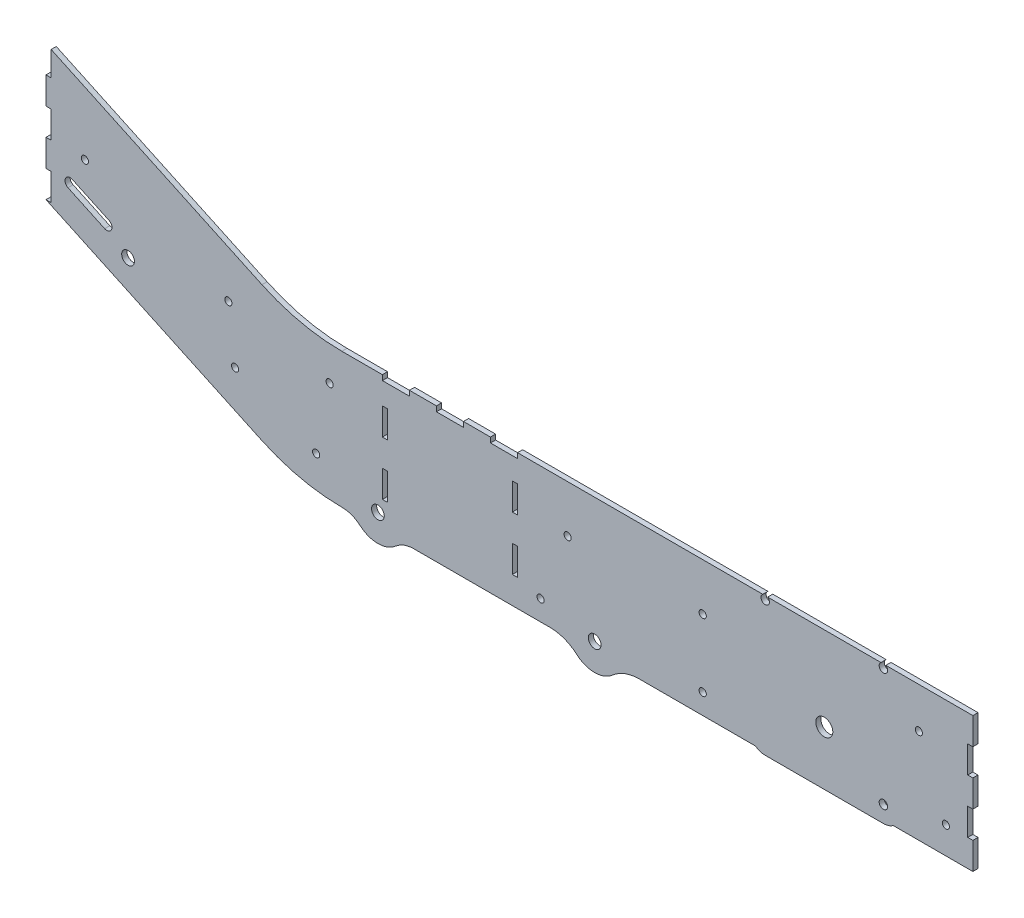
SolidWorks part; units mm, degrees
material "1060 Alloy"
ref_plane "Front Plane" through (0, 0, 0) normal (0, 0, 1) x (1, 0, 0)
ref_plane "Top Plane" through (0, 0, 0) normal (0, 1, 0) x (1, 0, 0)
ref_plane "Right Plane" through (0, 0, 0) normal (1, 0, 0) x (0, 0, -1)
sketch "Sketch1" plane through (0, 0, 0) normal (0, 0, 1) x (1, 0, 0)
  line L0 (255.5035, 390.3745) -> (331.7035, 390.3745)
  line L2 (-26.9148, 387.4343) -> (-61.4451, 403.5361)
  line L3 (-65.5242, 394.7884) -> (-30.9939, 378.6866)
  line L4 (-26.9148, 387.4343) -> (-61.4451, 403.5361)
  line L5 (-65.5242, 394.7884) -> (-30.9939, 378.6866)
  line L22 (790.1102, 263.3745) -> (790.1102, 288.7745)
  line L23 (790.1102, 288.7745) -> (785.2842, 288.7745)
  line L24 (785.2842, 288.7745) -> (785.2842, 314.1745)
  line L25 (785.2842, 314.1745) -> (790.1102, 314.1745)
  line L26 (790.1102, 314.1745) -> (790.1102, 339.5745)
  line L27 (790.1102, 339.5745) -> (785.2842, 339.5745)
  line L28 (785.2842, 339.5745) -> (785.2842, 364.9745)
  line L29 (785.2842, 364.9745) -> (790.1102, 364.9745)
  line L30 (790.1102, 364.9745) -> (790.1102, 390.3745)
  line L31 (790.1102, 390.3745) -> (331.7035, 390.3745)
  line L32 (116.862, 407.033) -> (-86.1898, 501.7176)
  line L33 (-86.1898, 501.7176) -> (-86.1898, 476.3176)
  line L34 (-86.1898, 476.3176) -> (-81.3638, 476.3176)
  line L35 (-81.3638, 476.3176) -> (-81.3638, 450.9176)
  line L36 (-81.3638, 450.9176) -> (-86.1898, 450.9176)
  line L37 (-86.1898, 450.9176) -> (-86.1898, 425.5176)
  line L38 (-86.1898, 425.5176) -> (-81.3638, 425.5176)
  line L39 (-81.3638, 425.5176) -> (-81.3638, 400.1176)
  line L40 (-81.3638, 400.1176) -> (-86.1898, 400.1176)
  line L41 (-86.1898, 400.1176) -> (-86.1898, 374.7176)
  line L42 (-86.1898, 374.7176) -> (116.862, 280.033)
  line L43 (666.755, 263.3745) -> (790.1102, 263.3745)
  line L44 (790.1102, 263.3745) -> (790.1102, 288.7745)
  line L45 (790.1102, 288.7745) -> (785.2842, 288.7745)
  line L46 (785.2842, 288.7745) -> (785.2842, 314.1745)
  line L47 (785.2842, 314.1745) -> (790.1102, 314.1745)
  line L48 (790.1102, 314.1745) -> (790.1102, 339.5745)
  line L49 (790.1102, 339.5745) -> (785.2842, 339.5745)
  line L50 (785.2842, 339.5745) -> (785.2842, 364.9745)
  line L51 (785.2842, 364.9745) -> (790.1102, 364.9745)
  line L52 (790.1102, 364.9745) -> (790.1102, 390.3745)
  line L53 (790.1102, 390.3745) -> (331.7035, 390.3745)
  line L54 (116.862, 407.033) -> (-86.1898, 501.7176)
  line L55 (-86.1898, 501.7176) -> (-86.1898, 476.3176)
  line L56 (-86.1898, 476.3176) -> (-81.3638, 476.3176)
  line L57 (-81.3638, 476.3176) -> (-81.3638, 450.9176)
  line L58 (-81.3638, 450.9176) -> (-86.1898, 450.9176)
  line L59 (-86.1898, 450.9176) -> (-86.1898, 425.5176)
  line L60 (-86.1898, 425.5176) -> (-81.3638, 425.5176)
  line L61 (-81.3638, 425.5176) -> (-81.3638, 400.1176)
  line L62 (-81.3638, 400.1176) -> (-86.1898, 400.1176)
  line L63 (-86.1898, 400.1176) -> (-86.1898, 374.7176)
  line L64 (-86.1898, 374.7176) -> (116.862, 280.033)
  line L65 (666.755, 263.3745) -> (790.1102, 263.3745)
  line L111 (259.7387, 263.3745) -> (387.7681, 263.3745)
  line L112 (259.7387, 263.3745) -> (387.7681, 263.3745)
  line L234 (471.6003, 263.3745) -> (624.4135, 263.3745)
  line L235 (471.6003, 263.3745) -> (624.4135, 263.3745)
  line L312 (306.3035, 385.5485) -> (306.3035, 390.3745)
  line L313 (306.3035, 385.5485) -> (306.3035, 390.3745) construction
  line L314 (306.3035, 390.3745) -> (280.9035, 390.3745)
  line L315 (306.3035, 390.3745) -> (280.9035, 390.3745)
  line L316 (280.9035, 390.3745) -> (280.9035, 385.5485)
  line L317 (280.9035, 390.3745) -> (280.9035, 385.5485) construction
  line L318 (280.9035, 385.5485) -> (255.5035, 385.5485)
  line L319 (280.9035, 385.5485) -> (255.5035, 385.5485) construction
  line L320 (255.5035, 385.5485) -> (255.5035, 390.3745)
  line L321 (255.5035, 385.5485) -> (255.5035, 390.3745) construction
  line L322 (255.5035, 390.3745) -> (192.0035, 390.3745)
  line L323 (255.5035, 390.3745) -> (192.0035, 390.3745)
  line L324 (331.7035, 390.3745) -> (331.7035, 385.5485)
  line L325 (331.7035, 390.3745) -> (331.7035, 385.5485) construction
  line L326 (331.7035, 385.5485) -> (306.3035, 385.5485)
  line L327 (331.7035, 385.5485) -> (306.3035, 385.5485) construction
  circle A1 centre (-51.9745, 393.795) radius 4.826
  arc A2 (116.862, 407.033) -> (192.0035, 390.3745) centre (192.0035, 568.1745) ccw
  arc A3 (116.862, 280.033) -> (192.0035, 263.3745) centre (192.0035, 441.1745) ccw
  arc A4 (116.862, 407.033) -> (192.0035, 390.3745) centre (192.0035, 568.1745) ccw
  arc A5 (116.862, 280.033) -> (192.0035, 263.3745) centre (192.0035, 441.1745) ccw
  circle A6 centre (-51.9745, 393.795) radius 4.826
  arc A8 (-30.9939, 378.6866) -> (-26.9148, 387.4343) centre (-28.9543, 383.0605) ccw
  arc A9 (-61.4451, 403.5361) -> (-65.5242, 394.7884) centre (-63.4846, 399.1622) ccw
  arc A10 (-30.9939, 378.6866) -> (-26.9148, 387.4343) centre (-28.9543, 383.0605) ccw
  arc A11 (-61.4451, 403.5361) -> (-65.5242, 394.7884) centre (-63.4846, 399.1622) ccw
  circle A15 centre (-51.9745, 393.795) radius 4.826
  circle A16 centre (-51.9745, 393.795) radius 4.826
  circle A17 centre (-51.9745, 393.795) radius 4.826
  circle A18 centre (-51.9745, 393.795) radius 4.826
  circle A19 centre (180.5102, 358.6245) radius 3.3782
  circle A20 centre (180.5102, 358.6245) radius 3.3782
  circle A21 centre (734.4842, 352.2745) radius 3.3782
  circle A22 centre (734.4842, 352.2745) radius 3.3782
  circle A23 centre (531.2588, 282.4245) radius 3.3782
  circle A24 centre (531.2588, 282.4245) radius 3.3782
  circle A25 centre (531.2588, 345.9245) radius 3.3782
  circle A26 centre (531.2588, 345.9245) radius 3.3782
  circle A27 centre (404.2588, 345.9245) radius 3.3782
  circle A28 centre (404.2588, 345.9245) radius 3.3782
  circle A29 centre (378.8588, 282.4245) radius 3.3782
  circle A30 centre (378.8588, 282.4245) radius 3.3782
  circle A31 centre (167.8102, 295.1245) radius 3.3782
  circle A32 centre (167.8102, 295.1245) radius 3.3782
  circle A33 centre (759.8842, 288.7745) radius 3.3782
  circle A34 centre (759.8842, 288.7745) radius 3.3782
  circle A35 centre (85.2602, 377.6745) radius 3.3782
  circle A36 centre (85.2602, 377.6745) radius 3.3782
  circle A37 centre (91.6102, 326.8745) radius 3.3782
  circle A38 centre (91.6102, 326.8745) radius 3.3782
  circle A39 centre (-49.6138, 425.5176) radius 3.3782
  circle A40 centre (-49.6138, 425.5176) radius 3.3782
  arc A50 (631.4704, 262.3745) -> (624.4135, 263.3745) centre (624.4135, 237.9745) ccw
  arc A51 (631.4704, 262.3745) -> (624.4135, 263.3745) centre (624.4135, 237.9745) ccw
  arc A52 (631.4704, 262.3745) -> (659.6981, 262.3745) centre (645.5842, 311.1745) ccw
  arc A53 (631.4704, 262.3745) -> (659.6981, 262.3745) centre (645.5842, 311.1745) ccw
  arc A54 (666.755, 263.3745) -> (659.6981, 262.3745) centre (666.755, 237.9745) ccw
  arc A55 (666.755, 263.3745) -> (659.6981, 262.3745) centre (666.755, 237.9745) ccw
  circle A95 centre (645.5842, 311.1745) radius 8 construction
  circle A96 centre (645.5842, 311.1745) radius 8
  arc A113 (412.9178, 253.8945) -> (387.7681, 263.3745) centre (387.7681, 225.2745) ccw
  arc A114 (412.9178, 253.8945) -> (387.7681, 263.3745) centre (387.7681, 225.2745) ccw
  arc A115 (412.9178, 253.8945) -> (446.4507, 253.8945) centre (429.6842, 272.9745) ccw
  arc A116 (412.9178, 253.8945) -> (446.4507, 253.8945) centre (429.6842, 272.9745) ccw
  arc A117 (471.6003, 263.3745) -> (446.4507, 253.8945) centre (471.6003, 225.2745) ccw
  arc A118 (471.6003, 263.3745) -> (446.4507, 253.8945) centre (471.6003, 225.2745) ccw
  circle A284 centre (429.6842, 272.9745) radius 6 construction
  circle A285 centre (429.6842, 272.9745) radius 6
  circle A472 centre (225.8711, 276.1495) radius 6 construction
  circle A473 centre (225.8711, 276.1495) radius 6
  circle A709 centre (-9.0329, 365.9221) radius 6 construction
  circle A710 centre (-9.0329, 365.9221) radius 6
  arc A735 (209.2445, 256.9475) -> (192.0035, 263.3745) centre (192.0035, 237.0358) ccw
  arc A736 (209.2445, 256.9475) -> (192.0035, 263.3745) centre (192.0035, 237.0358) ccw
  arc A737 (209.2445, 256.9475) -> (242.4976, 256.9475) centre (225.8711, 276.1495) ccw
  arc A738 (209.2445, 256.9475) -> (242.4976, 256.9475) centre (225.8711, 276.1495) ccw
  arc A739 (259.7387, 263.3745) -> (242.4976, 256.9475) centre (259.7387, 237.0358) ccw
  arc A740 (259.7387, 263.3745) -> (242.4976, 256.9475) centre (259.7387, 237.0358) ccw
  dimension "D1" = 0
  dimension "D2" = 0
  dimension "D3" = 0
  dimension "D6" = 0
  dimension "D7" = 0
  dimension "D8" = 0
  dimension "D9" = 0
  dimension "D10" = 0
  dimension "D11" = 0
  dimension "D12" = 0
  dimension "D13" = 0
  dimension "D14" = 0
  dimension "D15" = 0
  dimension "D16" = 0
  dimension "D17" = 0
  dimension "D18" = 0
extrude "Boss-Extrude1" add sketch "Sketch1" along normal blind 4.826
sketch "Sketch2" plane through (785.2842, 0, 0) normal (1, 0, 0) x (0, 0, -1)
  line L0 (0, 339.5745) -> (0, 364.9745) construction
  line L1 (0, 364.9745) -> (-4.826, 364.9745) construction
  line L2 (-4.826, 364.9745) -> (-4.826, 339.5745) construction
  line L3 (-4.826, 339.5745) -> (0, 339.5745) construction
  line L4 (0, 288.7745) -> (0, 314.1745) construction
  line L5 (0, 314.1745) -> (-4.826, 314.1745) construction
  line L6 (-4.826, 314.1745) -> (-4.826, 288.7745) construction
  line L7 (-4.826, 288.7745) -> (0, 288.7745) construction
  line L8 (0, 339.5745) -> (0, 364.9745)
  line L9 (0, 364.9745) -> (-4.826, 364.9745)
  line L10 (-4.826, 364.9745) -> (-4.826, 339.5745)
  line L11 (-4.826, 339.5745) -> (0, 339.5745)
  line L12 (0, 288.7745) -> (0, 314.1745)
  line L13 (0, 314.1745) -> (-4.826, 314.1745)
  line L14 (-4.826, 314.1745) -> (-4.826, 288.7745)
  line L15 (-4.826, 288.7745) -> (0, 288.7745)
extrude "Boss-Extrude2" add sketch "Sketch2" along normal up to surface (4.826 mm away) up to face at (790.1102, 377.6745, 2.413)
sketch "Sketch3" plane through (790.1102, 0, 0) normal (1, 0, 0) x (0, 0, -1)
  line L0 (-4.826, 263.3745) -> (-4.826, 390.3745) construction
  line L1 (-4.826, 390.3745) -> (0, 390.3745)
  line L2 (-4.826, 390.3745) -> (-4.826, 364.9745)
  line L3 (-4.826, 364.9745) -> (0, 364.9745)
  line L4 (0, 263.3745) -> (0, 390.3745)
  line L5 (0, 390.3745) -> (-4.826, 390.3745)
  line L6 (-4.826, 390.3745) -> (-4.826, 263.3745)
  line L7 (-4.826, 263.3745) -> (0, 263.3745)
  line L8 (0, 263.3745) -> (0, 390.3745)
  line L9 (0, 390.3745) -> (-4.826, 390.3745)
  line L10 (0, 390.3745) -> (0, 364.9745)
  line L11 (-4.826, 263.3745) -> (0, 263.3745)
  line L12 (-4.826, 339.5745) -> (0, 339.5745)
  line L13 (-4.826, 339.5745) -> (-4.826, 314.1745)
  line L14 (-4.826, 314.1745) -> (0, 314.1745)
  line L15 (0, 339.5745) -> (0, 314.1745)
  line L17 (-4.826, 288.7745) -> (0, 288.7745)
  line L18 (-4.826, 288.7745) -> (-4.826, 263.3745)
  line L19 (-4.826, 263.3745) -> (0, 263.3745)
  line L20 (0, 288.7745) -> (0, 263.3745)
  line L21 (-4.826, 288.7745) -> (0, 288.7745)
  line L22 (-4.826, 288.7745) -> (-4.826, 314.1745)
  line L23 (-4.826, 314.1745) -> (0, 314.1745)
  line L24 (0, 288.7745) -> (0, 314.1745)
  line L25 (-4.826, 339.5745) -> (0, 339.5745)
  line L26 (-4.826, 339.5745) -> (-4.826, 364.9745)
  line L27 (-4.826, 364.9745) -> (0, 364.9745)
  line L28 (0, 339.5745) -> (0, 364.9745)
  line M11 (0, 263.3745) -> (0, 390.3745)
  line M12 (0, 390.3745) -> (-4.826, 390.3745)
  line M13 (-4.826, 390.3745) -> (-4.826, 263.3745)
  line M14 (-4.826, 263.3745) -> (0, 263.3745)
  dimension "D1" = 0
extrude "Cut-Extrude1" cut sketch "Sketch3" against normal blind 4.826 contours L3 M13 M11 M12 | L14 L8 L12 M13 | L17 M13 M14 M11
sketch "Sketch4" plane through (-81.3638, 0, 0) normal (-1, 0, 0) x (0, 0, 1)
  line L0 (0, 476.3176) -> (0, 450.9176) construction
  line L1 (0, 450.9176) -> (4.826, 450.9176) construction
  line L2 (4.826, 450.9176) -> (4.826, 476.3176) construction
  line L3 (4.826, 476.3176) -> (0, 476.3176) construction
  line L4 (0, 425.5176) -> (0, 400.1176) construction
  line L5 (0, 400.1176) -> (4.826, 400.1176) construction
  line L6 (4.826, 400.1176) -> (4.826, 425.5176) construction
  line L7 (4.826, 425.5176) -> (0, 425.5176) construction
  line L8 (0, 476.3176) -> (0, 450.9176)
  line L9 (0, 450.9176) -> (4.826, 450.9176)
  line L10 (4.826, 450.9176) -> (4.826, 476.3176)
  line L11 (4.826, 476.3176) -> (0, 476.3176)
  line L12 (0, 425.5176) -> (0, 400.1176)
  line L13 (0, 400.1176) -> (4.826, 400.1176)
  line L14 (4.826, 400.1176) -> (4.826, 425.5176)
  line L15 (4.826, 425.5176) -> (0, 425.5176)
extrude "Boss-Extrude3" add sketch "Sketch4" along normal up to surface (4.826 mm away) up to face at (-86.1898, 489.0176, 2.413)
sketch "Sketch5" plane through (-86.1898, 0, 0) normal (-1, 0, 0) x (0, 0, 1)
  line L1 (4.826, 501.7176) -> (0, 501.7176)
  line L2 (4.826, 501.7176) -> (4.826, 476.3176)
  line L3 (4.826, 476.3176) -> (0, 476.3176)
  line L4 (0, 501.7176) -> (0, 374.7176)
  line L5 (0, 374.7176) -> (4.826, 374.7176)
  line L6 (4.826, 374.7176) -> (4.826, 501.7176)
  line L7 (4.826, 501.7176) -> (0, 501.7176)
  line L8 (0, 501.7176) -> (0, 374.7176)
  line L9 (0, 374.7176) -> (4.826, 374.7176)
  line L10 (0, 501.7176) -> (0, 476.3176)
  line L11 (4.826, 501.7176) -> (0, 501.7176)
  line L12 (4.826, 476.3176) -> (0, 476.3176)
  line L13 (4.826, 476.3176) -> (4.826, 450.9176)
  line L14 (4.826, 450.9176) -> (0, 450.9176)
  line L15 (0, 476.3176) -> (0, 450.9176)
  line L16 (4.826, 450.9176) -> (0, 450.9176)
  line L17 (4.826, 450.9176) -> (4.826, 425.5176)
  line L18 (4.826, 425.5176) -> (0, 425.5176)
  line L19 (0, 450.9176) -> (0, 425.5176)
  line L20 (4.826, 425.5176) -> (0, 425.5176)
  line L21 (4.826, 425.5176) -> (4.826, 400.1176)
  line L22 (4.826, 400.1176) -> (0, 400.1176)
  line L23 (0, 425.5176) -> (0, 400.1176)
  line L24 (4.826, 400.1176) -> (0, 400.1176)
  line L25 (4.826, 400.1176) -> (4.826, 374.7176)
  line L26 (4.826, 374.7176) -> (0, 374.7176)
  line L27 (0, 400.1176) -> (0, 374.7176)
  line M10 (0, 501.7176) -> (0, 374.7176)
  line M11 (0, 374.7176) -> (4.826, 374.7176)
  line M12 (4.826, 374.7176) -> (4.826, 501.7176)
  line M13 (4.826, 501.7176) -> (0, 501.7176)
  dimension "D1" = 0
extrude "Cut-Extrude2" cut sketch "Sketch5" against normal blind 4.826 contours L22 L8 M12 M11 | L18 L14 L8 M12 | L3 M12 M13 M10
sketch "Sketch6" plane through (790.1102, 0, 0) normal (1, 0, 0) x (0, 0, -1)
  line L0 (-4.826, 339.5745) -> (0, 339.5745) construction
  line L1 (0, 339.5745) -> (0, 364.9745) construction
  line L2 (0, 364.9745) -> (-4.826, 364.9745) construction
  line L3 (-4.826, 364.9745) -> (-4.826, 339.5745) construction
  line L4 (-4.826, 288.7745) -> (0, 288.7745) construction
  line L5 (0, 288.7745) -> (0, 314.1745) construction
  line L6 (0, 314.1745) -> (-4.826, 314.1745) construction
  line L7 (-4.826, 314.1745) -> (-4.826, 288.7745) construction
  line L8 (-4.826, 339.5745) -> (0, 339.5745)
  line L9 (0, 339.5745) -> (0, 364.9745)
  line L10 (0, 364.9745) -> (-4.826, 364.9745)
  line L11 (-4.826, 364.9745) -> (-4.826, 339.5745)
  line L12 (-4.826, 288.7745) -> (0, 288.7745)
  line L13 (0, 288.7745) -> (0, 314.1745)
  line L14 (0, 314.1745) -> (-4.826, 314.1745)
  line L15 (-4.826, 314.1745) -> (-4.826, 288.7745)
sketch "Sketch7" plane through (0, 0, 4.826) normal (0, 0, 1) x (1, 0, 0)
  line L0 (785.2842, 390.3745) -> (192.0035, 390.3745) construction
  line L1 (280.9035, 390.3745) -> (306.3035, 390.3745)
  line L2 (280.9035, 390.3745) -> (280.9035, 385.5485)
  line L3 (280.9035, 385.5485) -> (306.3035, 385.5485)
  line L4 (306.3035, 390.3745) -> (306.3035, 385.5485)
  line L5 (255.5035, 385.5485) -> (280.9035, 385.5485) construction
  line L6 (331.7035, 390.3745) -> (357.1035, 390.3745)
  line L7 (331.7035, 390.3745) -> (331.7035, 385.5485)
  line L8 (331.7035, 385.5485) -> (357.1035, 385.5485)
  line L9 (357.1035, 390.3745) -> (357.1035, 385.5485)
  line L10 (255.5035, 390.3745) -> (230.1035, 390.3745)
  line L11 (255.5035, 390.3745) -> (255.5035, 385.5485)
  line L12 (255.5035, 385.5485) -> (230.1035, 385.5485)
  line L13 (230.1035, 390.3745) -> (230.1035, 385.5485)
  line L14 (306.3035, 385.5485) -> (331.7035, 385.5485) construction
  point P14 (192.0035, 390.3745)
  dimension "D1" = 4.826
  dimension "D2" = 127
  dimension "D3" = 38.1
extrude "Cut-Extrude3" cut sketch "Sketch6" against normal blind 9.652
extrude "Cut-Extrude4" cut sketch "Sketch7" against normal through all
sketch "Sketch9" plane through (0, 0, 0) normal (0, 0, -1) x (-1, 0, 0)
  line L0 (-357.1035, 390.3745) -> (-357.1035, 364.9745) construction
  line L1 (-357.1035, 364.9745) -> (-352.2775, 364.9745)
  line L2 (-357.1035, 364.9745) -> (-357.1035, 339.5745)
  line L3 (-357.1035, 339.5745) -> (-352.2775, 339.5745)
  line L4 (-352.2775, 364.9745) -> (-352.2775, 339.5745)
  line L5 (-357.1035, 314.1745) -> (-352.2775, 314.1745)
  line L6 (-357.1035, 314.1745) -> (-357.1035, 288.7745)
  line L7 (-357.1035, 288.7745) -> (-352.2775, 288.7745)
  line L8 (-352.2775, 314.1745) -> (-352.2775, 288.7745)
  line L9 (-357.1035, 339.5745) -> (-357.1035, 314.1745) construction
  line L10 (-357.1035, 288.7745) -> (-357.1035, 263.3745) construction
  line L11 (-666.755, 263.3745) -> (-785.2842, 263.3745) construction
  line L12 (-293.6035, 385.5485) -> (-293.6035, 263.3745) construction
  line L13 (-280.9035, 385.5485) -> (-306.3035, 385.5485) construction
  line L14 (-230.1035, 339.5745) -> (-230.1035, 314.1745) construction
  line L15 (-234.9295, 314.1745) -> (-234.9295, 288.7745)
  line L16 (-230.1035, 288.7745) -> (-234.9295, 288.7745)
  line L17 (-230.1035, 314.1745) -> (-230.1035, 288.7745)
  line L18 (-230.1035, 314.1745) -> (-234.9295, 314.1745)
  line L19 (-234.9295, 364.9745) -> (-234.9295, 339.5745)
  line L20 (-230.1035, 339.5745) -> (-234.9295, 339.5745)
  line L21 (-230.1035, 364.9745) -> (-230.1035, 339.5745)
  line L22 (-230.1035, 364.9745) -> (-234.9295, 364.9745)
  dimension "D1" = 4.826
extrude "Cut-Extrude5" cut sketch "Sketch9" against normal through all
sketch "Sketch10" plane through (0, 0, 4.826) normal (0, 0, 1) x (1, 0, 0)
  line L0 (590.0471, 260.3745) -> (701.1721, 260.3745)
  line L1 (574.4642, 275.9574) -> (574.4642, 250.6745)
  line L2 (716.755, 275.9574) -> (716.755, 250.6745)
  line L37 (255.5035, 390.3745) -> (255.5035, 385.5485)
  line L38 (255.5035, 385.5485) -> (230.1035, 385.5485)
  line L39 (230.1035, 385.5485) -> (230.1035, 390.3745)
  line L40 (230.1035, 390.3745) -> (192.0035, 390.3745)
  line L41 (116.862, 407.033) -> (-81.3638, 499.4672)
  line L42 (-81.3638, 499.4672) -> (-81.3638, 476.3176)
  line L43 (-81.3638, 476.3176) -> (-86.1898, 476.3176)
  line L44 (-86.1898, 476.3176) -> (-86.1898, 450.9176)
  line L45 (-86.1898, 450.9176) -> (-81.3638, 450.9176)
  line L46 (-81.3638, 450.9176) -> (-81.3638, 425.5176)
  line L47 (-81.3638, 425.5176) -> (-86.1898, 425.5176)
  line L48 (-86.1898, 425.5176) -> (-86.1898, 400.1176)
  line L49 (-86.1898, 400.1176) -> (-81.3638, 400.1176)
  line L50 (-81.3638, 400.1176) -> (-81.3638, 374.7176)
  line L51 (-81.3638, 374.7176) -> (-86.1898, 374.7176)
  line L52 (-86.1898, 374.7176) -> (116.862, 280.033)
  line L53 (259.7387, 263.3745) -> (387.7681, 263.3745)
  line L54 (471.6003, 263.3745) -> (624.4135, 263.3745)
  line L55 (666.755, 263.3745) -> (785.2842, 263.3745)
  line L56 (785.2842, 263.3745) -> (785.2842, 288.7745)
  line L57 (785.2842, 288.7745) -> (780.4582, 288.7745)
  line L58 (780.4582, 288.7745) -> (780.4582, 314.1745)
  line L59 (780.4582, 314.1745) -> (785.2842, 314.1745)
  line L60 (785.2842, 314.1745) -> (785.2842, 339.5745)
  line L61 (785.2842, 339.5745) -> (780.4582, 339.5745)
  line L62 (780.4582, 339.5745) -> (780.4582, 364.9745)
  line L63 (780.4582, 364.9745) -> (785.2842, 364.9745)
  line L64 (785.2842, 364.9745) -> (785.2842, 390.3745)
  line L65 (785.2842, 390.3745) -> (357.1035, 390.3745)
  line L66 (357.1035, 390.3745) -> (357.1035, 385.5485)
  line L67 (357.1035, 385.5485) -> (331.7035, 385.5485)
  line L68 (331.7035, 385.5485) -> (331.7035, 390.3745)
  line L69 (331.7035, 390.3745) -> (306.3035, 390.3745)
  line L70 (306.3035, 390.3745) -> (306.3035, 385.5485)
  line L71 (306.3035, 385.5485) -> (280.9035, 385.5485)
  line L72 (280.9035, 385.5485) -> (280.9035, 390.3745)
  line L73 (280.9035, 390.3745) -> (255.5035, 390.3745)
  line L74 (255.5035, 390.3745) -> (255.5035, 385.5485)
  line L75 (255.5035, 385.5485) -> (230.1035, 385.5485)
  line L76 (230.1035, 385.5485) -> (230.1035, 390.3745)
  line L77 (230.1035, 390.3745) -> (192.0035, 390.3745)
  line L78 (116.862, 407.033) -> (-81.3638, 499.4672)
  line L79 (-81.3638, 499.4672) -> (-81.3638, 476.3176)
  line L80 (-81.3638, 476.3176) -> (-86.1898, 476.3176)
  line L81 (-86.1898, 476.3176) -> (-86.1898, 450.9176)
  line L82 (-86.1898, 450.9176) -> (-81.3638, 450.9176)
  line L83 (-81.3638, 450.9176) -> (-81.3638, 425.5176)
  line L84 (-81.3638, 425.5176) -> (-86.1898, 425.5176)
  line L85 (-86.1898, 425.5176) -> (-86.1898, 400.1176)
  line L86 (-86.1898, 400.1176) -> (-81.3638, 400.1176)
  line L87 (-81.3638, 400.1176) -> (-81.3638, 374.7176)
  line L88 (-81.3638, 374.7176) -> (-86.1898, 374.7176)
  line L89 (-86.1898, 374.7176) -> (116.862, 280.033)
  line L90 (259.7387, 263.3745) -> (387.7681, 263.3745)
  line L91 (471.6003, 263.3745) -> (624.4135, 263.3745)
  line L92 (666.755, 263.3745) -> (785.2842, 263.3745)
  line L93 (785.2842, 263.3745) -> (785.2842, 288.7745)
  line L94 (785.2842, 288.7745) -> (780.4582, 288.7745)
  line L95 (780.4582, 288.7745) -> (780.4582, 314.1745)
  line L96 (780.4582, 314.1745) -> (785.2842, 314.1745)
  line L97 (785.2842, 314.1745) -> (785.2842, 339.5745)
  line L98 (785.2842, 339.5745) -> (780.4582, 339.5745)
  line L99 (780.4582, 339.5745) -> (780.4582, 364.9745)
  line L100 (780.4582, 364.9745) -> (785.2842, 364.9745)
  line L101 (785.2842, 364.9745) -> (785.2842, 390.3745)
  line L102 (785.2842, 390.3745) -> (357.1035, 390.3745)
  line L103 (357.1035, 390.3745) -> (357.1035, 385.5485)
  line L104 (357.1035, 385.5485) -> (331.7035, 385.5485)
  line L105 (331.7035, 385.5485) -> (331.7035, 390.3745)
  line L106 (331.7035, 390.3745) -> (306.3035, 390.3745)
  line L107 (306.3035, 390.3745) -> (306.3035, 385.5485)
  line L108 (306.3035, 385.5485) -> (280.9035, 385.5485)
  line L109 (280.9035, 385.5485) -> (280.9035, 390.3745)
  line L110 (280.9035, 390.3745) -> (255.5035, 390.3745)
  arc A0 (701.1721, 260.3745) -> (716.755, 275.9574) centre (701.1721, 275.9574) ccw
  arc A1 (574.4642, 275.9574) -> (590.0471, 260.3745) centre (590.0471, 275.9574) ccw
  arc A2 (574.4642, 250.6745) -> (561.7642, 263.3745) centre (561.7642, 250.6745) ccw
  arc A3 (716.755, 250.6745) -> (729.455, 263.3745) centre (729.455, 250.6745) cw
  arc A11 (116.862, 407.033) -> (192.0035, 390.3745) centre (192.0035, 568.1745) ccw
  arc A12 (116.862, 280.033) -> (192.0035, 263.3745) centre (192.0035, 441.1745) ccw
  arc A13 (209.2445, 256.9475) -> (192.0035, 263.3745) centre (192.0035, 237.0358) ccw
  arc A14 (209.2445, 256.9475) -> (242.4976, 256.9475) centre (225.8711, 276.1495) ccw
  arc A15 (259.7387, 263.3745) -> (242.4976, 256.9475) centre (259.7387, 237.0358) ccw
  arc A16 (412.9178, 253.8945) -> (387.7681, 263.3745) centre (387.7681, 225.2745) ccw
  arc A17 (412.9178, 253.8945) -> (446.4507, 253.8945) centre (429.6842, 272.9745) ccw
  arc A18 (471.6003, 263.3745) -> (446.4507, 253.8945) centre (471.6003, 225.2745) ccw
  arc A19 (631.4704, 262.3745) -> (624.4135, 263.3745) centre (624.4135, 237.9745) ccw
  arc A20 (631.4704, 262.3745) -> (659.6981, 262.3745) centre (645.5842, 311.1745) ccw
  arc A21 (666.755, 263.3745) -> (659.6981, 262.3745) centre (666.755, 237.9745) ccw
  arc A22 (116.862, 407.033) -> (192.0035, 390.3745) centre (192.0035, 568.1745) ccw
  arc A23 (116.862, 280.033) -> (192.0035, 263.3745) centre (192.0035, 441.1745) ccw
  arc A24 (209.2445, 256.9475) -> (192.0035, 263.3745) centre (192.0035, 237.0358) ccw
  arc A25 (209.2445, 256.9475) -> (242.4976, 256.9475) centre (225.8711, 276.1495) ccw
  arc A26 (259.7387, 263.3745) -> (242.4976, 256.9475) centre (259.7387, 237.0358) ccw
  arc A27 (412.9178, 253.8945) -> (387.7681, 263.3745) centre (387.7681, 225.2745) ccw
  arc A28 (412.9178, 253.8945) -> (446.4507, 253.8945) centre (429.6842, 272.9745) ccw
  arc A29 (471.6003, 263.3745) -> (446.4507, 253.8945) centre (471.6003, 225.2745) ccw
  arc A30 (631.4704, 262.3745) -> (624.4135, 263.3745) centre (624.4135, 237.9745) ccw
  arc A31 (631.4704, 262.3745) -> (659.6981, 262.3745) centre (645.5842, 311.1745) ccw
  arc A32 (666.755, 263.3745) -> (659.6981, 262.3745) centre (666.755, 237.9745) ccw
  dimension "D2" = 12.7
  dimension "D3" = 12.7
  dimension "D1" = 0
extrude "Boss-Extrude4" add sketch "Sketch10" against normal up to surface (4.826 mm away) contours L92 A32 A31 L0 A0 L2 A3 | A31 A30 L91 A2 L1 A1 L0
sketch "Sketch11" plane through (0, 0, 4.826) normal (0, 0, 1) x (1, 0, 0)
  circle A0 centre (590.0471, 387.0824) radius 4
  circle A1 centre (701.1721, 387.0824) radius 4
  circle A2 centre (701.1721, 275.9574) radius 4
  circle A3 centre (590.0471, 240.9779) radius 4
  dimension "D1" = 8
extrude "Cut-Extrude6" cut sketch "Sketch11" against normal through all
equation "\"w\"= .19"
equation "\"D1@Boss-Extrude1\"=\"w\""
equation "\"D1@Cut-Extrude1\"=\"w\""
equation "\"D1@Cut-Extrude2\"=\"w\""
equation "\"D1@Sketch7\"=\"w\""
equation "\"D1@Cut-Extrude3\"=\"w\"*2"
equation "\"D1@Sketch9\"=\"w\""
